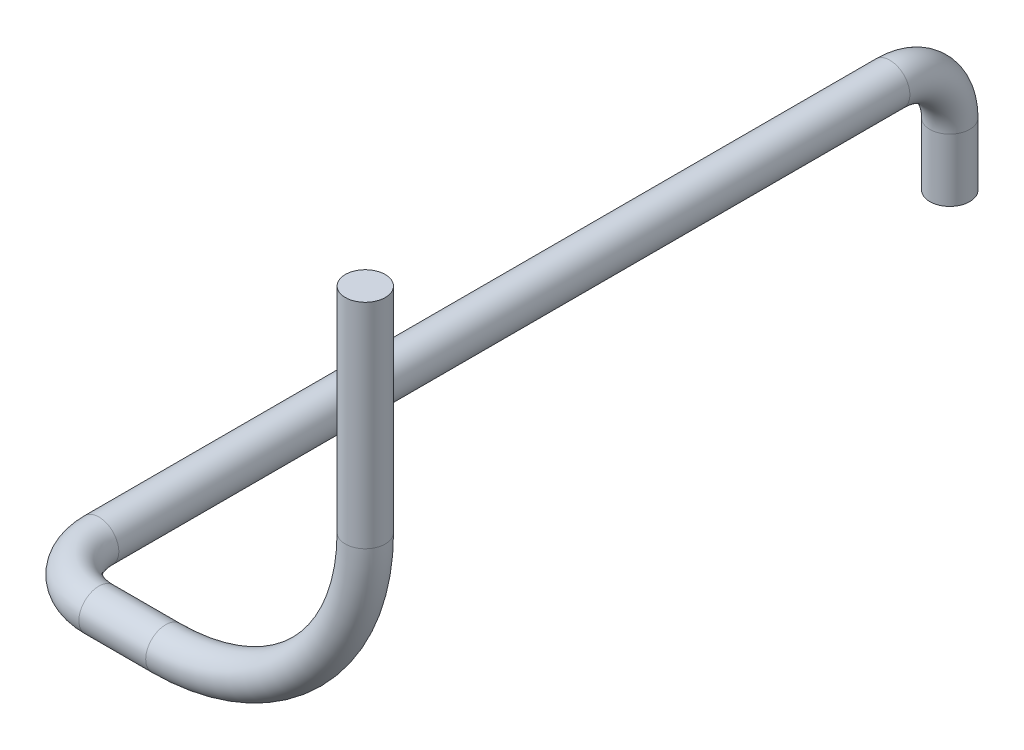
SolidWorks part; units mm, degrees
ref_plane "Front Plane" through (0, 0, 0) normal (0, 0, 1) x (1, 0, 0)
ref_plane "Top Plane" through (0, 0, 0) normal (0, 1, 0) x (1, 0, 0)
ref_plane "Right Plane" through (0, 0, 0) normal (1, 0, 0) x (0, 0, -1)
sketch "Sketch1" plane through (0, 0, 0) normal (0, 0, 1) x (1, 0, 0)
  line L0 (0, 0) -> (0, -10.6945)
  line L1 (-10, -20.6945) -> (-12.5084, -20.6945)
  arc A0 (0, -10.6945) -> (-10, -20.6945) centre (-10, -10.6945) cw
  point P6 (-12.5084, -20.6945)
  dimension "D1" = 10
ref_plane "Plane1" through (0, -20.6945, 0) normal (0, 1, 0) x (1, 0, 0)
sketch "Sketch2" plane through (0, -20.6945, 0) normal (0, 1, 0) x (1, 0, 0)
  line L0 (-12.5084, 0) -> (-13.3482, 0)
  line L1 (-10, 0) -> (-12.5084, 0) construction
  line L2 (-16.3482, 3) -> (-16.3482, 39.9166)
  arc A0 (-13.3482, 0) -> (-16.3482, 3) centre (-13.3482, 3) cw
  point P5 (-16.3482, 39.9166)
  dimension "D1" = 3
sketch "Sketch3" plane through (0, 0, 0) normal (0, 1, 0) x (1, 0, 0)
  circle A0 centre (0, 0) radius 1
  dimension "D1" = 2
sweep "Sweep1" add profiles "Sketch3" path "Sketch1"
sketch "Sketch4" plane through (-12.5084, 0, 0) normal (-1, 0, 0) x (0, 0, 1)
  circle A1 centre (0, -20.6945) radius 1
  circle A2 centre (0, -20.6945) radius 1
  dimension "D1" = 0
sweep "Sweep2" add profiles "Sketch4" path "Sketch2"
ref_point "Point1"
ref_plane "Plane2" through (-16.3482, 0, 0) normal (1, 0, 0) x (0, 0, -1)
sketch "Sketch5" plane through (-16.3482, 0, 0) normal (1, 0, 0) x (0, 0, -1)
  line L0 (39.9166, -20.6945) -> (42.6295, -20.6945)
  line L1 (45.6295, -23.6945) -> (45.6295, -26.8313)
  line L2 (10.0915, -20.6945) -> (-10.0915, -20.6945) construction
  arc A0 (42.6295, -20.6945) -> (45.6295, -23.6945) centre (42.6295, -23.6945) cw
  point P3 (46.5157, -26.0729)
  point P7 (41.6377, -20.6945)
  point P10 (44.6683, -24.4953)
  point P11 (45.6295, -26.8313)
  dimension "D1" = 3
sketch "Sketch6" plane through (0, 0, -39.9166) normal (0, 0, -1) x (-1, 0, 0)
  circle A1 centre (16.3482, -20.6945) radius 1
  circle A2 centre (16.3482, -20.6945) radius 1
  dimension "D1" = 0
sweep "Sweep3" add profiles "Sketch6" path "Sketch5"
